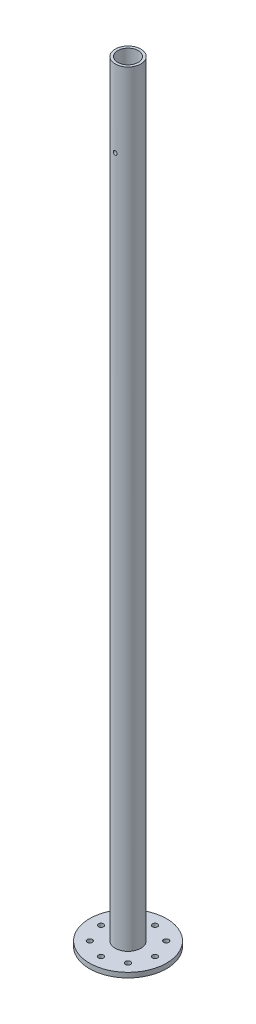
SolidWorks part; units mm, degrees
material "AISI 316 Annealed Stainless Steel Bar (SS)"
ref_plane "Front" through (0, 0, 0) normal (0, 0, 1) x (1, 0, 0)
ref_plane "Top" through (0, 0, 0) normal (0, 1, 0) x (1, 0, 0)
ref_plane "Right" through (0, 0, 0) normal (1, 0, 0) x (0, 0, -1)
sketch "Sketch1" plane through (0, 0, 0) normal (0, 1, 0) x (1, 0, 0)
  circle A0 centre (0, 0) radius 13.32
  circle A1 centre (0, 0) radius 16.7
  dimension "D1" = 33.4
  dimension "D2" = 3.38
extrude "Boss-Extrude1" add sketch "Sketch1" along normal blind 1000
sketch "Sketch2" plane through (0, 1000, 0) normal (0, 1, 0) x (1, 0, 0)
  line L0 (-9.5, 8.124) -> (9.5, 8.124)
  arc A0 (9.5, 8.124) -> (-9.5, 8.124) centre (0, 0) ccw
  dimension "D1" = 25
  dimension "D2" = 19
extrude "Cut-Extrude1" [suppressed] cut sketch "Sketch2" against normal blind 300
sketch3d "3DSketch1"
  circle A0 centre (0, 970, 0) radius 12.5
  point P2 (0, 957.5, 0)
  dimension "D1" = 25
curve "Helix/Spiral1" [suppressed] pitch 710 height 177.5 turns 0.25
hole_wizard "#8 (0.199) Diameter Hole4" [suppressed] positions "3DSketch8" profile "Sketch12" hole size "#8" standard "ANSI Inch"
sketch3d "3DSketch8"
  point P22 (0, 970, -16.7)
sketch "Sketch12" plane through (0, 970, -16.7) normal (1, 0, 0) x (0, 1, 0)
  line L0 (0, 0) -> (0, 40)
  line L1 (0, 40) -> (2.5273, 40)
  line L2 (2.5273, 40) -> (2.5273, 0)
  line L5 (2.5273, 0) -> (0, 0)
  line L10 (0, 40) -> (-2.5273, 40) construction
  line L11 (0, -6.35) -> (0, 107.95) construction
  dimension "Hole Dia." = 5.0546
  dimension "Hole Depth" = 40
  dimension "Drill Angle" = 180
pattern_curve "CrvPattern1" [suppressed] parameters "D1"=9, "D3"=50, "D2"=1, "D4"=50
sketch "Sketch13" plane through (0, 0, 0) normal (0, -1, 0) x (-1, 0, 0)
  circle A0 centre (0, 0) radius 50
  circle A1 centre (0, 0) radius 16.7
  dimension "D1" = 100
  dimension "D2" = 33.4
extrude "Boss-Extrude2" add sketch "Sketch13" against normal blind 6.35
sketch "Sketch18" plane through (0, 0, 0) normal (0, -1, 0) x (-1, 0, 0)
  line L0 (-59.3466, -59.3466) -> (-19.0222, -19.0222) construction
  line L1 (21.1748, -21.1748) -> (10.3579, -10.3579) construction
  line L2 (20.7157, 0) -> (-54.5366, 0) construction
  dimension "D1" = 45
  dimension "D2" = 90
hole_wizard "1/4 Clearance Hole1" positions "Sketch15" profile "Sketch14" hole size "1/4" standard "ANSI Inch"
sketch "Sketch15" plane through (0, 0, 0) normal (0, -1, 0) x (-1, 0, 0)
  line L0 (-50, 0) -> (50, 0) construction
  line L1 (0, 50) -> (0, -50) construction
  line L2 (141442.531, -141442.531) -> (-141410.9984, 141410.9984) construction
  line L3 (-141480.7028, -141480.7028) -> (141402.3341, 141402.3341) construction
  point P0 (-35, 0)
  point P2 (0, 35)
  point P4 (35, 0)
  point P6 (0, -35)
  point P13 (24.7487, 24.7487)
  point P15 (24.7487, -24.7487)
  point P17 (-24.7487, -24.7487)
  point P19 (-24.7487, 24.7487)
  dimension "D1" = 35
  dimension "D2" = 35
  dimension "D3" = 35
  dimension "D4" = 35
  dimension "D5" = 35
  dimension "D6" = 35
  dimension "D7" = 35
  dimension "D8" = 35
sketch "Sketch14" plane through (35, 0, 0) normal (1, 0, 0) x (0, 0, -1)
  line L0 (0, 0) -> (0, 50)
  line L1 (0, 50) -> (3.3782, 50)
  line L2 (3.3782, 50) -> (3.3782, 0)
  line L5 (3.3782, 0) -> (0, 0)
  line L10 (0, 50) -> (-3.3782, 50) construction
  line L11 (0, -6.35) -> (0, 107.95) construction
  dimension "Hole Dia." = 6.7564
  dimension "Hole Depth" = 50
  dimension "Drill Angle" = 180
hole_wizard "#8 (0.199) Diameter Hole6" positions "3DSketch9" profile "Sketch17" hole size "#8" standard "ANSI Inch"
sketch3d "3DSketch9"
  point P0 (0, 900, -16.7)
  dimension "D1" = 100
sketch "Sketch17" plane through (0, 900, -16.7) normal (1, 0, 0) x (0, 1, 0)
  line L0 (0, 0) -> (0, 50)
  line L1 (0, 50) -> (2.5273, 50)
  line L2 (2.5273, 50) -> (2.5273, 0)
  line L5 (2.5273, 0) -> (0, 0)
  line L10 (0, 50) -> (-2.5273, 50) construction
  line L11 (0, -6.35) -> (0, 107.95) construction
  dimension "Hole Dia." = 5.0546
  dimension "Hole Depth" = 50
  dimension "Drill Angle" = 180
